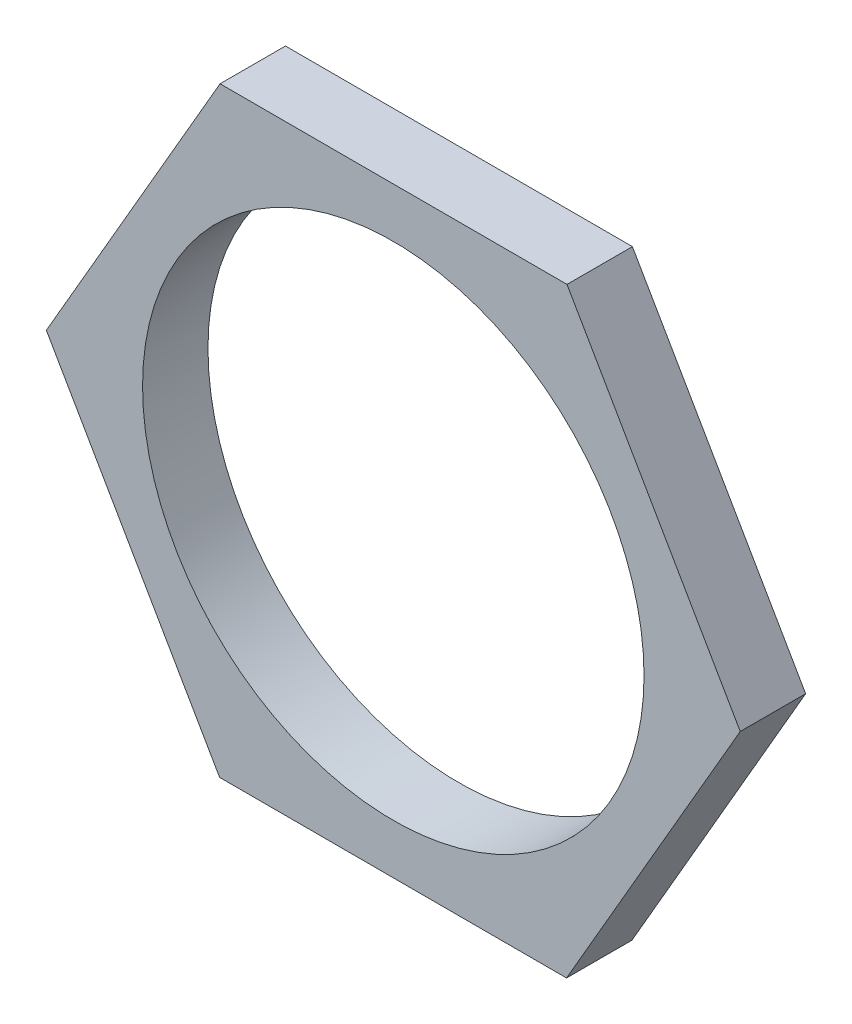
SolidWorks part; units mm, degrees
ref_plane "Alzado" through (0, 0, 0) normal (0, 0, 1) x (1, 0, 0)
ref_plane "Planta" through (0, 0, 0) normal (0, 1, 0) x (1, 0, 0)
ref_plane "Vista lateral" through (0, 0, 0) normal (1, 0, 0) x (0, 0, -1)
sketch "Croquis1" plane through (0, 0, 0) normal (0, 0, 1) x (1, 0, 0)
  line L1 (7.967, 13.7742) -> (-7.9453, 13.7867)
  line L2 (-7.9453, 13.7867) -> (-15.9123, 0.0125)
  line L3 (-15.9123, 0.0125) -> (-7.967, -13.7742)
  line L4 (-7.967, -13.7742) -> (7.9453, -13.7867)
  line L5 (7.9453, -13.7867) -> (15.9123, -0.0125)
  line L6 (15.9123, -0.0125) -> (7.967, 13.7742)
  circle A0 centre (0, 0) radius 11.5
  circle A1 centre (0, 0) radius 13.7805 construction
  dimension "D1" = 23
extrude "Saliente-Extruir1" add sketch "Croquis1" along normal blind 3
